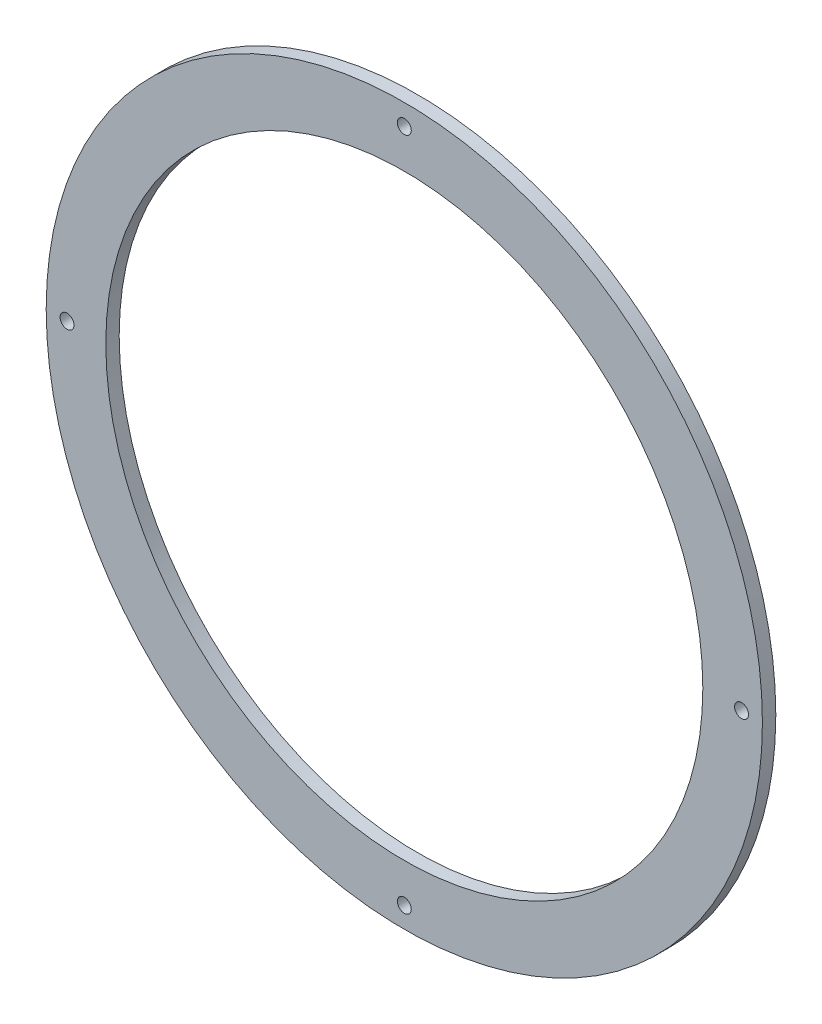
SolidWorks part; units mm, degrees
material "NBR"
ref_plane "Front Plane" through (0, 0, 0) normal (0, 0, 1) x (1, 0, 0)
ref_plane "Top Plane" through (0, 0, 0) normal (0, 1, 0) x (1, 0, 0)
ref_plane "Right Plane" through (0, 0, 0) normal (1, 0, 0) x (0, 0, -1)
sketch "Sketch1" plane through (0, 0, 0) normal (0, 0, 1) x (1, 0, 0)
  circle A3 centre (0, 0) radius 84.9312
  circle A4 centre (0, 0) radius 70.7948
extrude "Boss-Extrude1" add sketch "Sketch1" along normal blind 3.175
sketch "Sketch2" plane through (0, 0, 3.175) normal (0, 0, 1) x (1, 0, 0)
  line L0 (0, 0) -> (0, -84.9312) construction
  circle A1 centre (0, 0) radius 84.9312 construction
  circle A2 centre (0, 0) radius 81.6292
  circle A3 centre (0, 0) radius 81.6292 construction
  circle A4 centre (0, -79.9783) radius 1.651
  circle A5 centre (0, 0) radius 79.9783 construction
  circle A6 centre (-79.9783, 0) radius 1.651
  circle A7 centre (0, 79.9783) radius 1.651
  circle A8 centre (79.9783, 0) radius 1.651
  point P19 (0, 0)
  dimension "D2" = 3.302
  dimension "D1" = 3.302
  dimension "D3" = 4
extrude "Cut-Extrude1" cut sketch "Sketch2" against normal up to surface (3.175 mm away) up to face at (84.9312, 0, 0)
